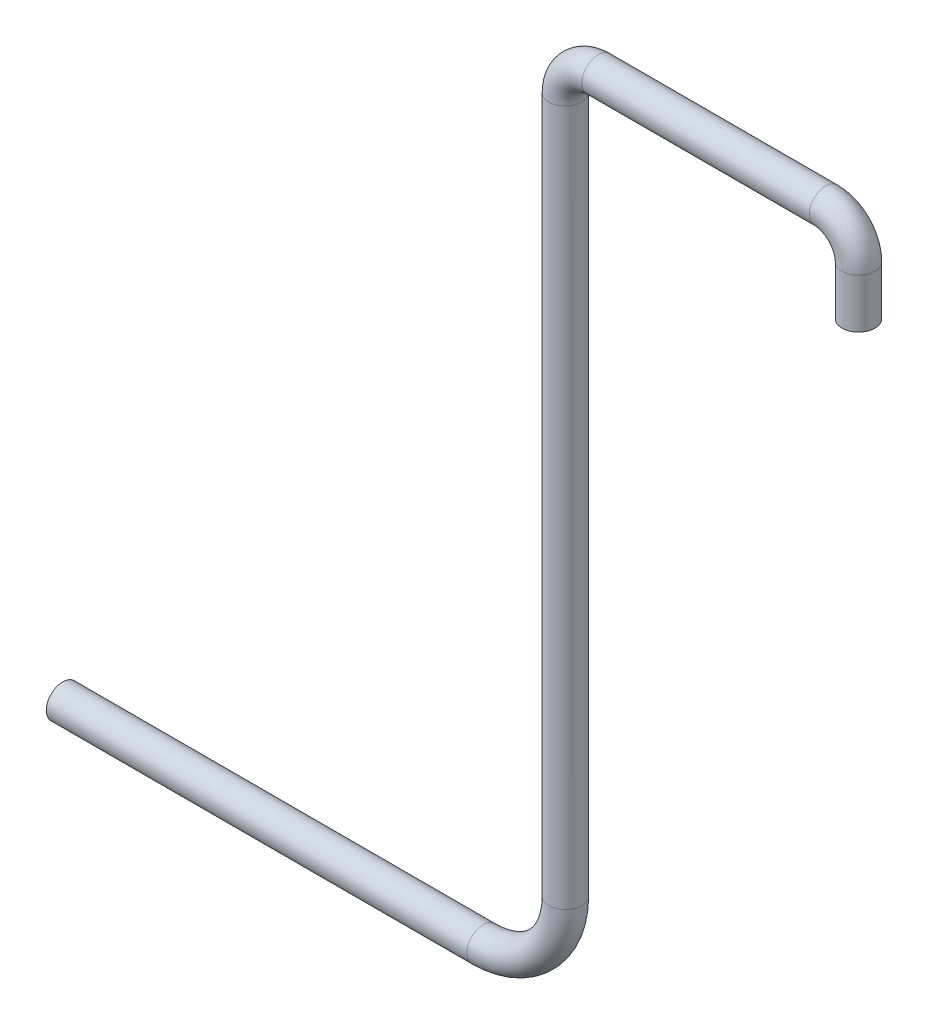
SolidWorks part; units mm, degrees
ref_plane "Plan de face" through (0, 0, 0) normal (0, 0, 1) x (1, 0, 0)
ref_plane "Plan de dessus" through (0, 0, 0) normal (0, 1, 0) x (1, 0, 0)
ref_plane "Plan de droite" through (0, 0, 0) normal (1, 0, 0) x (0, 0, -1)
sketch "Esquisse1" plane through (0, 0, 0) normal (0, 0, 1) x (1, 0, 0)
  line L0 (0, 0) -> (0, 0.3)
  line L1 (-0.2, 0.5) -> (-1.5845, 0.5)
  line L2 (-1.7845, 0.3) -> (-1.7845, -3.9371)
  line L3 (-2.2845, -4.4371) -> (-4.8451, -4.4371)
  arc A0 (-1.7845, 0.3) -> (-1.5845, 0.5) centre (-1.5845, 0.3) cw
  arc A1 (-0.2, 0.5) -> (0, 0.3) centre (-0.2, 0.3) cw
  arc A2 (-2.2845, -4.4371) -> (-1.7845, -3.9371) centre (-2.2845, -3.9371) ccw
  dimension "D1" = 0.2
  dimension "D2" = 0.5
sketch "Esquisse2" plane through (0, 0, 0) normal (0, 1, 0) x (1, 0, 0)
  circle A0 centre (0, 0) radius 0.1
sweep "Balayage1" add profiles "Esquisse2" path "Esquisse1"
